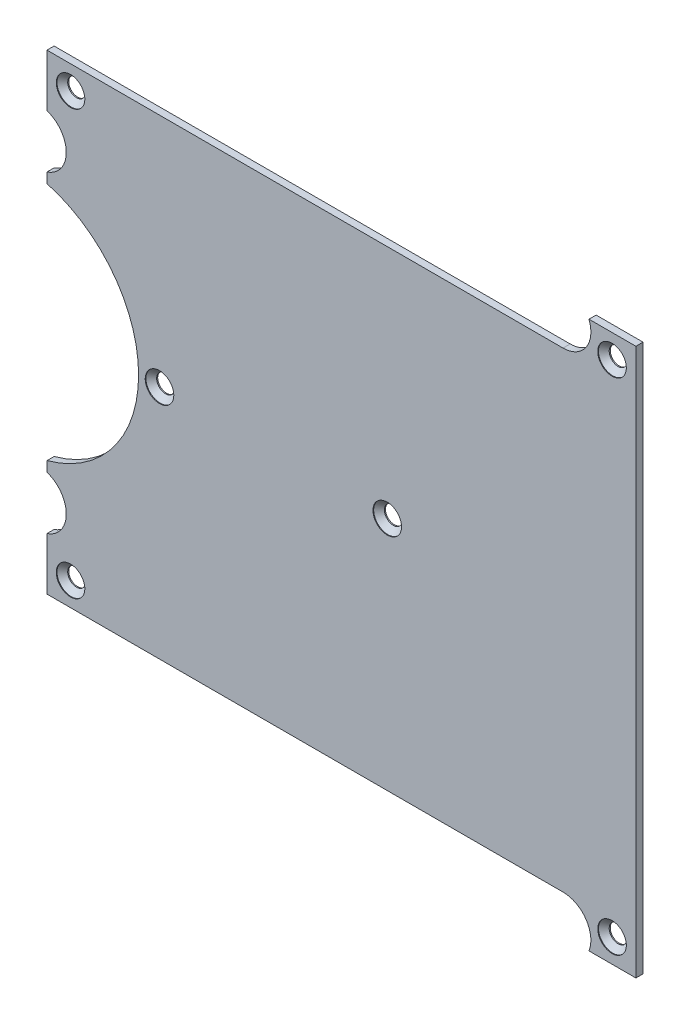
SolidWorks part; units mm, degrees
ref_plane "Front Plane" through (0, 0, 0) normal (0, 0, 1) x (1, 0, 0)
ref_plane "Top Plane" through (0, 0, 0) normal (0, 1, 0) x (1, 0, 0)
ref_plane "Right Plane" through (0, 0, 0) normal (1, 0, 0) x (0, 0, -1)
sketch "Sketch1" plane through (0, 0, 0) normal (0, 0, 1) x (1, 0, 0)
  line L19 (10.2, -38.3) -> (10.2, 38.3)
  line L20 (3.6323, -38.3) -> (10.2, -38.3)
  line L21 (-72.252, -32.98) -> (0, -32.98)
  line L22 (-72.252, -25.6308) -> (-72.252, -32.98)
  line L23 (-72.252, -16.7891) -> (-72.252, -18.2092)
  line L24 (-72.252, 18.2092) -> (-72.252, 16.7891)
  line L25 (-72.252, 32.98) -> (-72.252, 25.6308)
  line L26 (0, 32.98) -> (-72.252, 32.98)
  line L27 (10.2, 38.3) -> (3.6323, 38.3)
  line L28 (10.2, -38.3) -> (10.2, 38.3)
  line L29 (3.6323, -38.3) -> (10.2, -38.3)
  line L30 (-72.252, -32.98) -> (0, -32.98)
  line L31 (-72.252, -25.6308) -> (-72.252, -32.98)
  line L32 (-72.252, -16.7891) -> (-72.252, -18.2092)
  line L33 (-72.252, 18.2092) -> (-72.252, 16.7891)
  line L34 (-72.252, 32.98) -> (-72.252, 25.6308)
  line L35 (0, 32.98) -> (-72.252, 32.98)
  line L36 (10.2, 38.3) -> (3.6323, 38.3)
  circle A7 centre (-68.952, 29.68) radius 1.25
  circle A8 centre (6.8632, 35) radius 1.25
  circle A9 centre (6.8632, -35) radius 1.25
  circle A10 centre (-68.952, -29.68) radius 1.25
  arc A14 (3.6323, -38.3) -> (0, -32.98) centre (0, -36.88) ccw
  arc A15 (-72.252, -25.6308) -> (-72.252, -18.2092) centre (-73.452, -21.92) ccw
  arc A16 (-72.252, -16.7891) -> (-72.252, 16.7891) centre (-76.822, 0) ccw
  arc A17 (-72.252, 18.2092) -> (-72.252, 25.6308) centre (-73.452, 21.92) ccw
  arc A18 (0, 32.98) -> (3.6323, 38.3) centre (0, 36.88) ccw
  arc A19 (3.6323, -38.3) -> (0, -32.98) centre (0, -36.88) ccw
  arc A20 (-72.252, -25.6308) -> (-72.252, -18.2092) centre (-73.452, -21.92) ccw
  arc A21 (-72.252, -16.7891) -> (-72.252, 16.7891) centre (-76.822, 0) ccw
  arc A22 (-72.252, 18.2092) -> (-72.252, 25.6308) centre (-73.452, 21.92) ccw
  arc A23 (0, 32.98) -> (3.6323, 38.3) centre (0, 36.88) ccw
  circle A46 centre (-56.497, 0) radius 1.25
  circle A47 centre (-24.611, 0) radius 1.25
  dimension "D2" = 2.5
  dimension "D1" = 0.2
extrude "Shape" add sketch "Sketch1" along normal blind 1
hole_wizard "CSK for M2 Flat Head Machine Screw1" positions "Sketch2" profile "Sketch3" countersink size "M2" standard "ANSI Metric" end condition through all
sketch "Sketch2" plane through (0, 0, 1) normal (0, 0, 1) x (1, 0, 0)
  point P0 (-68.952, 29.68)
  point P3 (6.8632, 35)
  point P6 (6.8632, -35)
  point P9 (-68.952, -29.68)
  point P13 (-56.497, 0)
  point P16 (-24.611, 0)
sketch "Sketch3" plane through (-68.952, 29.68, 1) normal (1, 0, 0) x (0, -1, 0)
  line L0 (0, 0) -> (0, 1)
  line L1 (0, 1) -> (1, 1)
  line L2 (1, 1) -> (1, 1.1)
  line L3 (1, 1.1) -> (2, 0.1)
  line L4 (2, 0.1) -> (2, 0)
  line L6 (2, 0) -> (0, 0)
  line L7 (-1, 1.1) -> (-2, 0.1) construction
  line L11 (0, -6.35) -> (0, 107.95) construction
  dimension "Thru Hole Dia." = 2
  dimension "Thru Hole Depth" = 1
  dimension "C'Sink Dia." = 4
  dimension "C'Sink Angle" = 90
  dimension "Head Clearance" = 0.1
